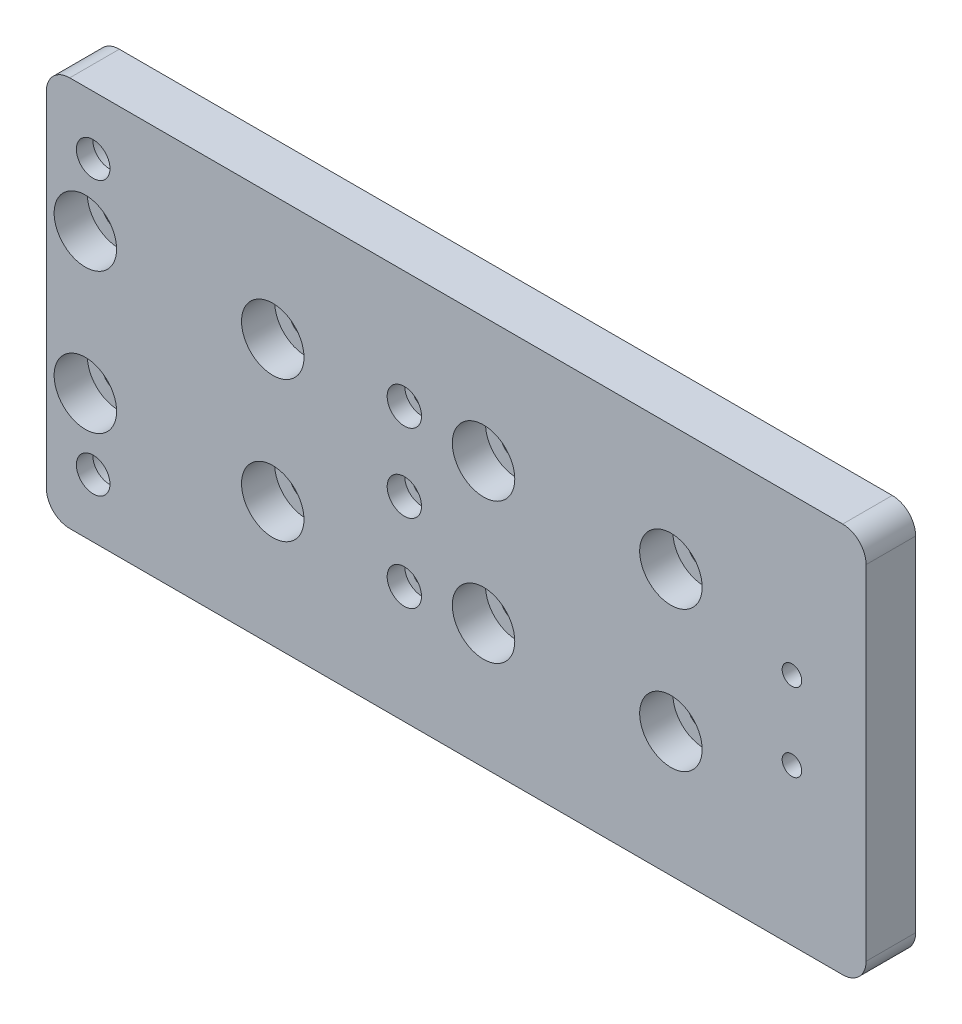
SolidWorks part; units mm, degrees
ref_plane "Plano frontal" through (0, 0, 0) normal (0, 0, 1) x (1, 0, 0)
ref_plane "Plano superior" through (0, 0, 0) normal (0, 1, 0) x (1, 0, 0)
ref_plane "Plano direito" through (0, 0, 0) normal (1, 0, 0) x (0, 0, -1)
ref_plane "Plano1" through (0, 0, 6.35) normal (0, 0, 1) x (1, 0, 0)
sketch "Esboço1" plane through (0, 0, 6.35) normal (0, 0, 1) x (1, 0, 0)
  line L0 (0, 37) -> (0, -13)
  line L1 (0, -13) -> (105, -13)
  line L2 (105, -13) -> (105, 37)
  line L3 (105, 37) -> (0, 37)
  dimension "D1" = 105
  dimension "D2" = 50
extrude "Ressalto-extrusão1" add sketch "Esboço1" against normal blind 6.35
hole_wizard "Furo de diâmetro Ø2.5 (2.5)1" positions "Esboço3" profile "Esboço2" hole size "Ø2.5" standard "Ansi Metric"
sketch "Esboço3" plane through (0, 0, 0) normal (0, 0, -1) x (-1, 0, 0)
  point P0 (-95.5, 17)
  point P1 (-95.5, 7)
sketch "Esboço2" plane through (95.5, 17, 0) normal (1, 0, 0) x (0, 1, 0)
  line L0 (0, 0) -> (0, 6.35)
  line L1 (0, 6.35) -> (1.25, 6.35)
  line L2 (1.25, 6.35) -> (1.25, 0)
  line L5 (1.25, 0) -> (0, 0)
  line L11 (0, -6.35) -> (0, 107.95) construction
  dimension "Thru Hole Dia." = 2.5
  dimension "Thru Hole Depth" = 6.35
hole_wizard "Rebaixo para parafuso de máquina de cabeça sextavada de M21" positions "Esboço5" profile "Esboço4" counterbore size "M2" standard "Ansi Metric"
sketch "Esboço5" plane through (0, 0, 6.35) normal (0, 0, 1) x (1, 0, 0)
  point P0 (45.856, 22)
  point P1 (45.856, 2)
  point P2 (45.856, 12)
sketch "Esboço4" plane through (45.856, 22, 6.35) normal (1, 0, 0) x (0, -1, 0)
  line L0 (0, 0) -> (0, 6.35)
  line L1 (0, 6.35) -> (1.1, 6.35)
  line L3 (1.1, 6.35) -> (1.1, 2.25)
  line L4 (1.1, 2.25) -> (2.2, 2.25)
  line L5 (2.2, 2.25) -> (2.2, 0)
  line L7 (2.2, 0) -> (0, 0)
  line L11 (0, -6.35) -> (0, 107.95) construction
  dimension "Thru Hole Dia." = 2.2
  dimension "Thru Hole Depth" = 6.35
  dimension "C'Bore Dia." = 4.4
  dimension "C'Bore Depth" = 2.25
hole_wizard "Rebaixo para parafuso de máquina de cabeça sextavada de M41" positions "Esboço7" profile "Esboço6" counterbore size "M4" standard "Ansi Metric" end condition through all
sketch "Esboço7" plane through (0, 0, 0) normal (0, 0, -1) x (-1, 0, 0)
  point P0 (-6, -5.5)
  point P1 (-6, 29.5)
  point P2 (-71, -1.5)
  point P3 (-71, 25.5)
  point P4 (0, 0)
  point P5 (0, 0)
sketch "Esboço6" plane through (6, -5.5, 0) normal (1, 0, 0) x (0, 1, 0)
  line L0 (0, 0) -> (0, 6.35)
  line L1 (0, 6.35) -> (2.15, 6.35)
  line L3 (2.15, 6.35) -> (2.15, 4.25)
  line L4 (2.15, 4.25) -> (4, 4.25)
  line L5 (4, 4.25) -> (4, 0)
  line L7 (4, 0) -> (0, 0)
  line L11 (0, -6.35) -> (0, 107.95) construction
  dimension "Thru Hole Dia." = 4.3
  dimension "Thru Hole Depth" = 6.35
  dimension "C'Bore Dia." = 8
  dimension "C'Bore Depth" = 4.25
hole_wizard "Rebaixo para parafuso de máquina de cabeça sextavada de M42" positions "Esboço9" profile "Esboço8" counterbore size "M4" standard "Ansi Metric"
sketch "Esboço9" plane through (0, 0, 6.35) normal (0, 0, 1) x (1, 0, 0)
  point P0 (5, 21)
  point P1 (5, 3)
  point P2 (29, 3)
  point P3 (29, 21)
  point P4 (56, 3)
  point P5 (56, 21)
  point P6 (80, 21)
  point P7 (80, 3)
sketch "Esboço8" plane through (5, 21, 6.35) normal (1, 0, 0) x (0, -1, 0)
  line L0 (0, 0) -> (0, 6.35)
  line L1 (0, 6.35) -> (2.15, 6.35)
  line L3 (2.15, 6.35) -> (2.15, 4.25)
  line L4 (2.15, 4.25) -> (4, 4.25)
  line L5 (4, 4.25) -> (4, 0)
  line L7 (4, 0) -> (0, 0)
  line L11 (0, -6.35) -> (0, 107.95) construction
  dimension "Thru Hole Dia." = 4.3
  dimension "Thru Hole Depth" = 6.35
  dimension "C'Bore Dia." = 8
  dimension "C'Bore Depth" = 4.25
fillet "Filete1" radius 3 4 edges at (0, 37, 3.175) (105, 37, 3.175) (0, -13, 3.175) (105, -13, 3.175)
sketch "Esboço11" plane through (0, 0, 0) normal (0, 0, -1) x (-1, 0, 0)
  circle A0 centre (-71, -1.5) radius 4
  circle A1 centre (-71, 25.5) radius 4
extrude "Ressalto-extrusão2" add sketch "Esboço11" against normal blind 6.35
